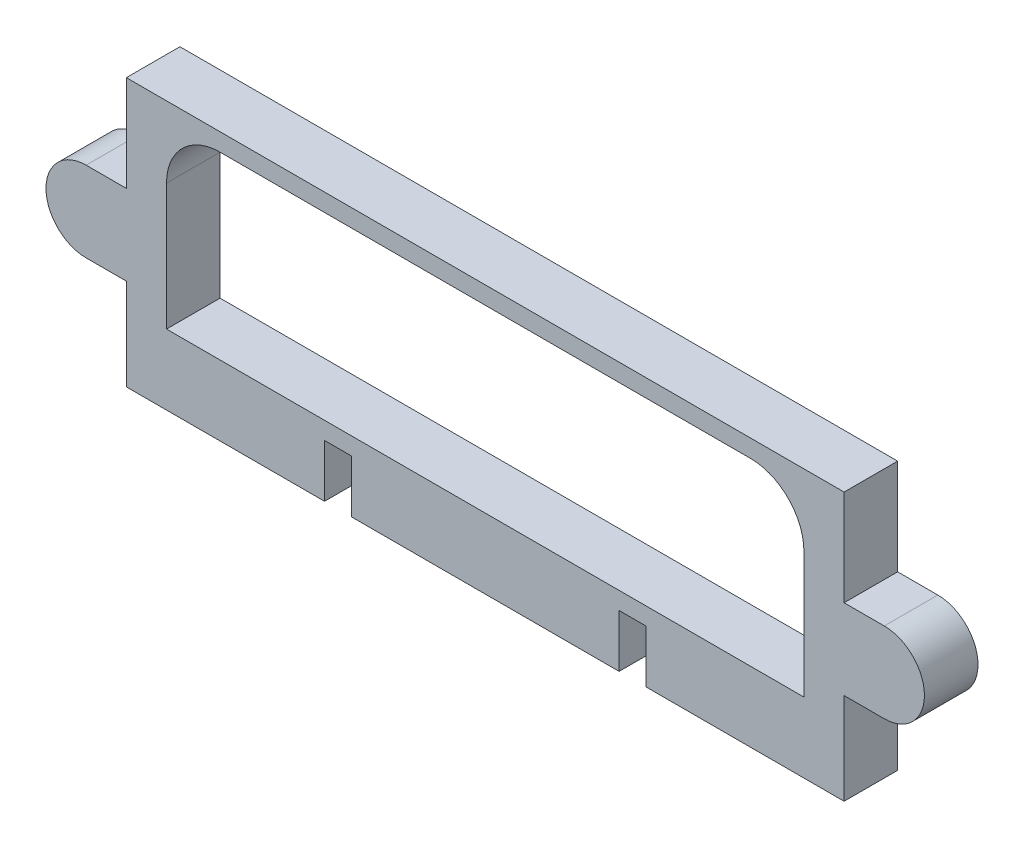
SolidWorks part; units mm, degrees
ref_plane "Alzado" through (0, 0, 0) normal (0, 0, 1) x (1, 0, 0)
ref_plane "Planta" through (0, 0, 0) normal (0, 1, 0) x (1, 0, 0)
ref_plane "Vista lateral" through (0, 0, 0) normal (1, 0, 0) x (0, 0, -1)
sketch "Croquis1" plane through (0, 0, 0) normal (0, 0, 1) x (1, 0, 0)
  line L0 (-25, 0) -> (25, 0)
  line L1 (-25, 0) -> (-25, 9.8443)
  line L2 (-25, 9.8443) -> (-30, 9.8443)
  line L3 (-30, 9.8443) -> (-30, 0)
  line L4 (-30, 0) -> (-67, 0)
  line L5 (-67, 0) -> (-67, 17.0976)
  line L6 (-67, 50) -> (67, 50)
  line L7 (0, 0) -> (0, 50) construction
  line L8 (67, 0) -> (67, 17.0976)
  line L9 (30, 0) -> (67, 0)
  line L10 (30, 9.8443) -> (30, 0)
  line L11 (25, 9.8443) -> (30, 9.8443)
  line L12 (25, 0) -> (25, 9.8443)
  line L13 (-59.4222, 24.5976) -> (-59.5, 24.5976) construction
  line L15 (-59.5, 13.1) -> (-59.5, 36.7)
  line L16 (-49.5, 46.7) -> (44.1, 46.7)
  line L18 (-59.4222, 17.0976) -> (-59.5, 17.0976)
  line L19 (-59.4222, 32.0976) -> (-59.5, 32.0976)
  line L20 (-67, 32.0976) -> (-74.5, 32.0976)
  line L21 (-67, 17.0976) -> (-74.5, 17.0976)
  line L22 (67, 32.0976) -> (74.5, 32.0976)
  line L24 (-67, 32.0976) -> (-67, 50)
  line L25 (67, 17.0976) -> (74.5, 17.0976)
  line L26 (67, 32.0976) -> (67, 50)
  line L28 (-59.5, 13.1) -> (59.5, 13.1)
  line L29 (59.5, 13.1) -> (59.5, 36.7)
  line L30 (49.5, 46.7) -> (44.1, 46.7)
  arc A1 (-59.5, 36.7) -> (-49.5, 46.7) centre (-49.5, 36.7) cw
  arc A3 (-74.5, 32.0976) -> (-74.5, 17.0976) centre (-74.5, 24.5976) ccw
  arc A4 (74.5, 32.0976) -> (74.5, 17.0976) centre (74.5, 24.5976) cw
  arc A5 (59.5, 36.7) -> (49.5, 46.7) centre (49.5, 36.7) ccw
  point P4 (0, 0)
  point P22 (54.1, 46.7)
  point P27 (-67, 25.6815)
  dimension "D11" = 7.5
  dimension "D12" = 15
  dimension "D5" = 10
  dimension "D1" = 50
  dimension "D2" = 37
  dimension "D3" = 5
  dimension "D4" = 50
  dimension "D7" = 7.5
  dimension "D8" = 3.3
  dimension "D10" = 7.5
extrude "Saliente-Extruir1" add sketch "Croquis1" along normal blind 10
